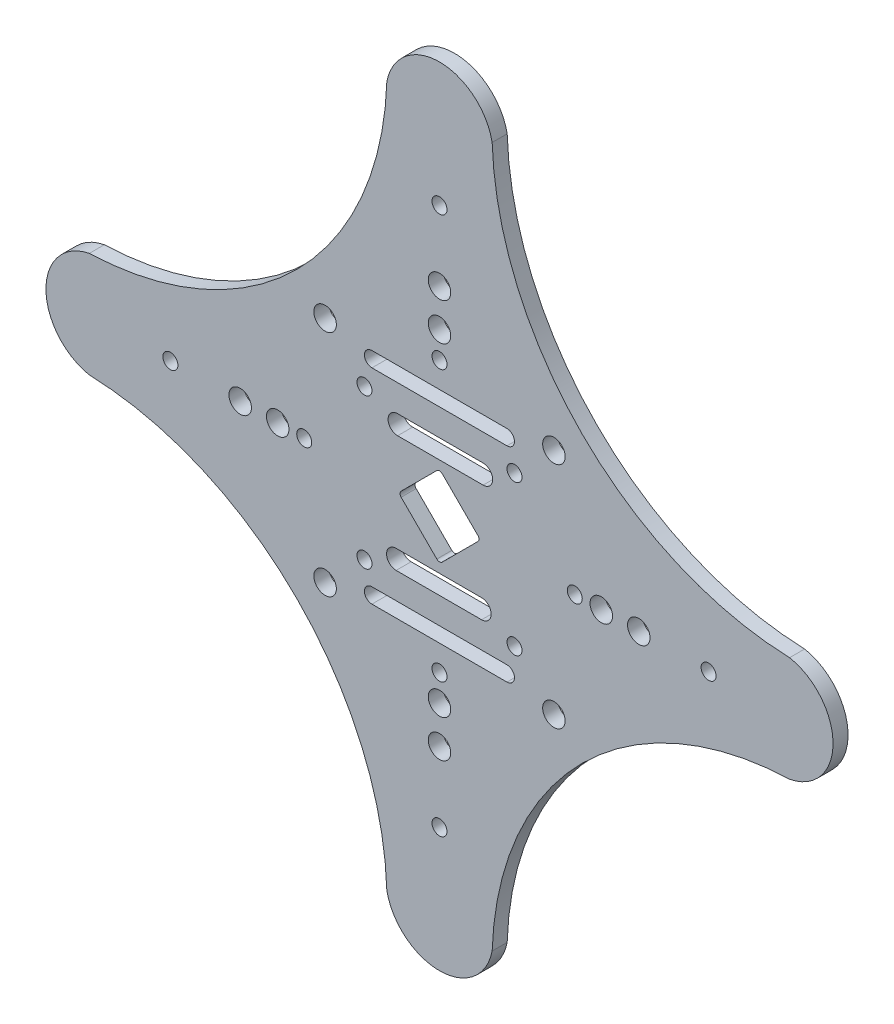
SolidWorks part; units mm, degrees
ref_plane "前视基准面" through (0, 0, 0) normal (0, 0, 1) x (1, 0, 0)
ref_plane "上视基准面" through (0, 0, 0) normal (0, 1, 0) x (1, 0, 0)
ref_plane "右视基准面" through (0, 0, 0) normal (1, 0, 0) x (0, 0, -1)
sketch "Model" plane through (0, 0, 0) normal (0, 0, 1) x (1, 0, 0)
  line L0 (152.3985, 91.0069) -> (141.0047, 91.0069)
  line L1 (141.0047, 93.554) -> (152.3985, 93.554)
  line L2 (152.5997, 109.1993) -> (141.2059, 109.1993)
  line L3 (141.2059, 106.6522) -> (152.5997, 106.6522)
  line L4 (151.8986, 100.4934) -> (147.1408, 105.2512)
  line L5 (146.4337, 105.2512) -> (141.6759, 100.4934)
  line L6 (141.6759, 99.7863) -> (146.4337, 95.0285)
  line L7 (147.1408, 95.0285) -> (151.8986, 99.7863)
  line L8 (137.7799, 87.5035) -> (155.7799, 87.5035)
  line L9 (155.7799, 85.5035) -> (137.7799, 85.5035)
  line L10 (137.7799, 112.7762) -> (155.7799, 112.7762)
  line L11 (155.7799, 114.7762) -> (137.7799, 114.7762)
  circle A0 centre (156.7872, 110.1398) radius 1
  circle A1 centre (136.7872, 110.1398) radius 1
  circle A2 centre (136.7872, 90.1398) radius 1
  circle A3 centre (156.7872, 90.1398) radius 1
  circle A4 centre (168.354, 100.1398) radius 1.5
  circle A5 centre (146.7872, 121.7066) radius 1.5
  circle A6 centre (125.2205, 100.1398) radius 1.5
  circle A7 centre (146.7872, 78.5731) radius 1.5
  circle A8 centre (146.7872, 126.7066) radius 1.5
  circle A9 centre (120.2205, 100.1398) radius 1.5
  circle A10 centre (146.7872, 73.5731) radius 1.5
  circle A11 centre (173.354, 100.1398) radius 1.5
  circle A12 centre (146.7872, 118.171) radius 1
  circle A13 centre (128.756, 100.1398) radius 1
  circle A14 centre (146.7872, 82.1086) radius 1
  circle A15 centre (164.8184, 100.1398) radius 1
  arc A16 (165.7942, 119.1469) -> (193.458, 107.1597) centre (194.7856, 148.1382) ccw
  arc A17 (153.8071, 146.8106) -> (165.7942, 119.1469) centre (194.7856, 148.1382) ccw
  arc A18 (127.7802, 119.1469) -> (139.7673, 146.8106) centre (98.7888, 148.1382) ccw
  arc A19 (100.1164, 107.1597) -> (127.7802, 119.1469) centre (98.7888, 148.1382) ccw
  arc A20 (127.7802, 81.1328) -> (100.1164, 93.1199) centre (98.7888, 52.1414) ccw
  arc A21 (139.7673, 53.469) -> (127.7802, 81.1328) centre (98.7888, 52.1414) ccw
  arc A22 (165.7942, 81.1328) -> (153.8071, 53.469) centre (194.7856, 52.1414) ccw
  arc A23 (193.458, 93.1199) -> (165.7942, 81.1328) centre (194.7856, 52.1414) ccw
  arc A24 (193.458, 93.1199) -> (193.458, 107.1597) centre (192.0936, 100.1398) ccw
  arc A25 (153.8071, 146.8106) -> (139.7673, 146.8106) centre (146.7872, 145.4462) ccw
  arc A26 (100.1164, 107.1597) -> (100.1164, 93.1199) centre (101.4808, 100.1398) ccw
  arc A27 (139.7673, 53.469) -> (153.8071, 53.469) centre (146.7872, 54.8334) ccw
  circle A28 centre (162.0372, 115.3898) radius 1.5
  circle A29 centre (131.5372, 115.3898) radius 1.5
  circle A30 centre (131.5372, 84.8898) radius 1.5
  circle A31 centre (162.0372, 84.8898) radius 1.5
  arc A32 (139.7312, 92.2804) -> (141.0047, 91.0069) centre (141.0047, 92.2804) ccw
  arc A33 (152.3985, 91.0069) -> (152.3985, 93.554) centre (152.3985, 92.2804) ccw
  arc A34 (141.0047, 93.554) -> (139.7312, 92.2804) centre (141.0047, 92.2804) ccw
  arc A35 (141.2059, 109.1993) -> (139.9324, 107.9258) centre (141.2059, 107.9258) ccw
  arc A36 (152.5997, 106.6522) -> (152.5997, 109.1993) centre (152.5997, 107.9258) ccw
  arc A37 (139.9324, 107.9258) -> (141.2059, 106.6522) centre (141.2059, 107.9258) ccw
  arc A38 (151.8986, 99.7863) -> (151.8986, 100.4934) centre (151.545, 100.1398) ccw
  arc A39 (147.1408, 105.2512) -> (146.4337, 105.2512) centre (146.7872, 104.8976) ccw
  arc A40 (141.6759, 100.4934) -> (141.6759, 99.7863) centre (142.0294, 100.1398) ccw
  arc A41 (146.4337, 95.0285) -> (147.1408, 95.0285) centre (146.7872, 95.382) ccw
  circle A42 centre (182.6572, 100.1398) radius 1
  circle A43 centre (146.7872, 136.0369) radius 1
  circle A44 centre (110.9172, 100.1398) radius 1
  circle A45 centre (146.7872, 64.2428) radius 1
  arc A46 (137.7799, 87.5035) -> (136.7799, 86.5035) centre (137.7799, 86.5035) ccw
  arc A47 (155.7799, 85.5035) -> (155.7799, 87.5035) centre (155.7799, 86.5035) ccw
  arc A48 (136.7799, 86.5035) -> (137.7799, 85.5035) centre (137.7799, 86.5035) ccw
  arc A49 (136.7799, 113.7762) -> (137.7799, 112.7762) centre (137.7799, 113.7762) ccw
  arc A50 (155.7799, 112.7762) -> (155.7799, 114.7762) centre (155.7799, 113.7762) ccw
  arc A51 (137.7799, 114.7762) -> (136.7799, 113.7762) centre (137.7799, 113.7762) ccw
  spline S0 degree 3 poles (0, 0) (0.3333, 0) (0.6667, 0) (1, 0) knots 0 0 0 0 1 1 1 1
  spline S1 degree 3 poles (0, 0) (0.3333, 0) (0.6667, 0) (1, 0) knots 0 0 0 0 1 1 1 1
extrude "凸台-拉伸1" add sketch "Model" along normal blind 2 contours S0 S1 | A6 | A5 | A4 | A3 | A2 | A1 | A0 | A14 | A13 | A12 | A11 | A10 | A9 | A8 | A7 | A16 A24 A23 A22 A27 A21 A20 A26 A19 A18 A25 A17 | A15 | A31 | A30 | A29 | A28 | L4 A39 L5 A40 L6 A41 L7 A38 | L2 A35 A37 L3 A36 | L0 A32 A34 L1 A33 | A45 | A44 | A43 | A42 | L10 A50 L11 A51 A49 | L8 A47 L9 A48 A46
